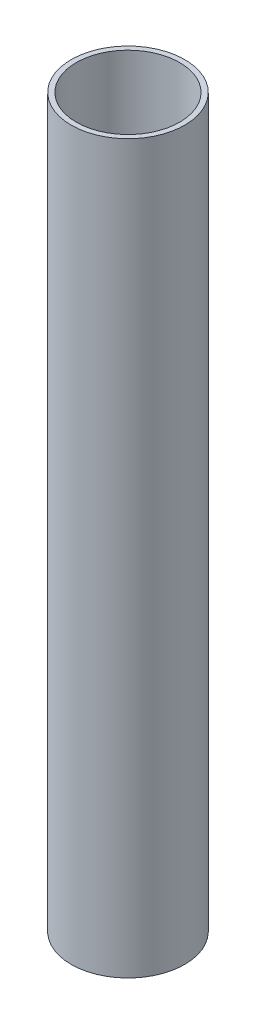
SolidWorks part; units mm, degrees
ref_plane "Front Plane" through (0, 0, 0) normal (0, 0, 1) x (1, 0, 0)
ref_plane "Top Plane" through (0, 0, 0) normal (0, 1, 0) x (1, 0, 0)
ref_plane "Right Plane" through (0, 0, 0) normal (1, 0, 0) x (0, 0, -1)
sketch "Sketch1" plane through (0, 0, 0) normal (0, 1, 0) x (1, 0, 0)
  circle A0 centre (0, 0) radius 7.9375
  circle A1 centre (0, 0) radius 7.2263
  dimension "D1" = 15.875
  dimension "D2" = 14.4526
extrude "Boss-Extrude1" add sketch "Sketch1" along normal blind 101.6
